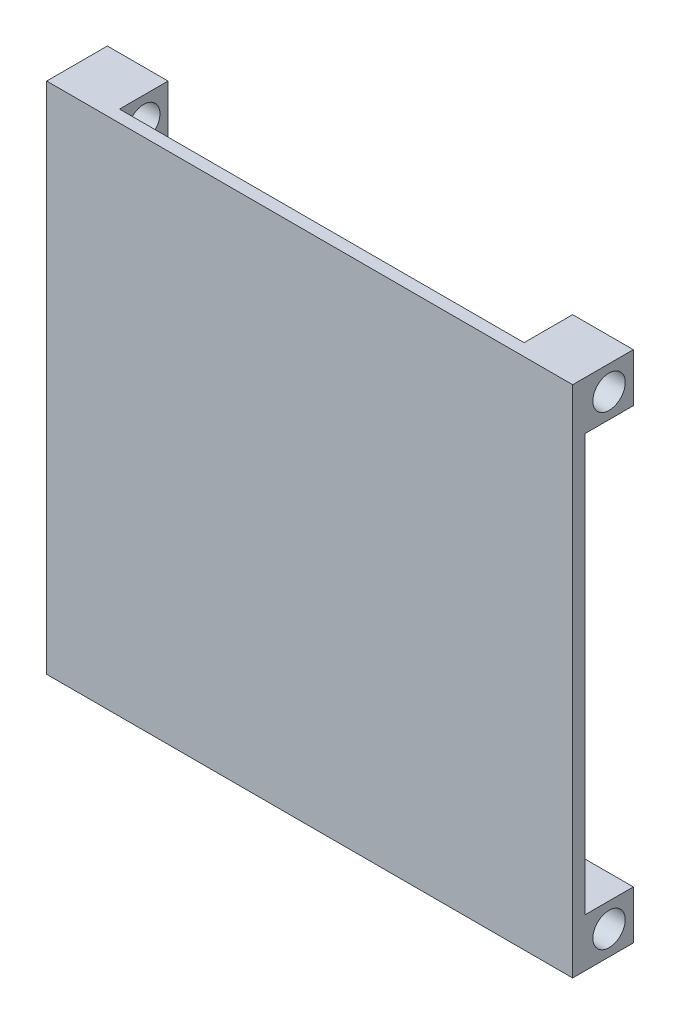
SolidWorks part; units mm, degrees
ref_plane "Plan de face" through (0, 0, 0) normal (0, 0, 1) x (1, 0, 0)
ref_plane "Plan de dessus" through (0, 0, 0) normal (0, 1, 0) x (1, 0, 0)
ref_plane "Plan de droite" through (0, 0, 0) normal (1, 0, 0) x (0, 0, -1)
sketch "Esquisse1" plane through (0, 0, 0) normal (0, 0, 1) x (1, 0, 0)
  line L1 (0, 0) -> (-130, 0)
  line L2 (0, 0) -> (0, 127)
  line L3 (0, 127) -> (-130, 127)
  line L4 (-130, 0) -> (-130, 127)
  dimension "D1" = 127
  dimension "D2" = 130
extrude "Boss.-Extru.1" add sketch "Esquisse1" along normal blind 3
sketch "Esquisse2" plane through (0, 0, 0) normal (1, 0, 0) x (0, 0, -1)
  line L0 (0, 63.5) -> (32.2297, 63.5) construction
  line L1 (0, 0) -> (0, 127) construction
  line L2 (12, 0) -> (12, 12)
  line L3 (0, 127) -> (12, 127)
  line L4 (0, 127) -> (0, 115)
  line L5 (0, 115) -> (12, 115)
  line L6 (12, 127) -> (12, 115)
  line L7 (0, 12) -> (12, 12)
  line L8 (0, 0) -> (0, 12)
  line L9 (0, 0) -> (12, 0)
  circle A0 centre (6, 121) radius 4
  circle A1 centre (6, 6) radius 4
  dimension "D1" = 8
  dimension "D2" = 57.5
  dimension "D3" = 6
  dimension "D4" = 6
  dimension "D5" = 6
  dimension "D6" = 6
extrude "Boss.-Extru.2" add sketch "Esquisse2" against normal blind 130
sketch "Esquisse3" plane through (0, 127, 0) normal (0, 1, 0) x (1, 0, 0)
  line L0 (-130, 12) -> (0, 12) construction
  line L1 (-115, 12) -> (-15, 12)
  line L2 (-115, 12) -> (-115, 0)
  line L3 (-115, 0) -> (-15, 0)
  line L4 (-15, 12) -> (-15, 0)
  line L5 (0, 0) -> (-130, 0) construction
  line L6 (-130, 12) -> (-130, -3) construction
  line L7 (0, 12) -> (0, -3) construction
  dimension "D1" = 15
  dimension "D2" = 15
extrude "Enlèv. mat.-Extru.1" cut sketch "Esquisse3" against normal blind 160
